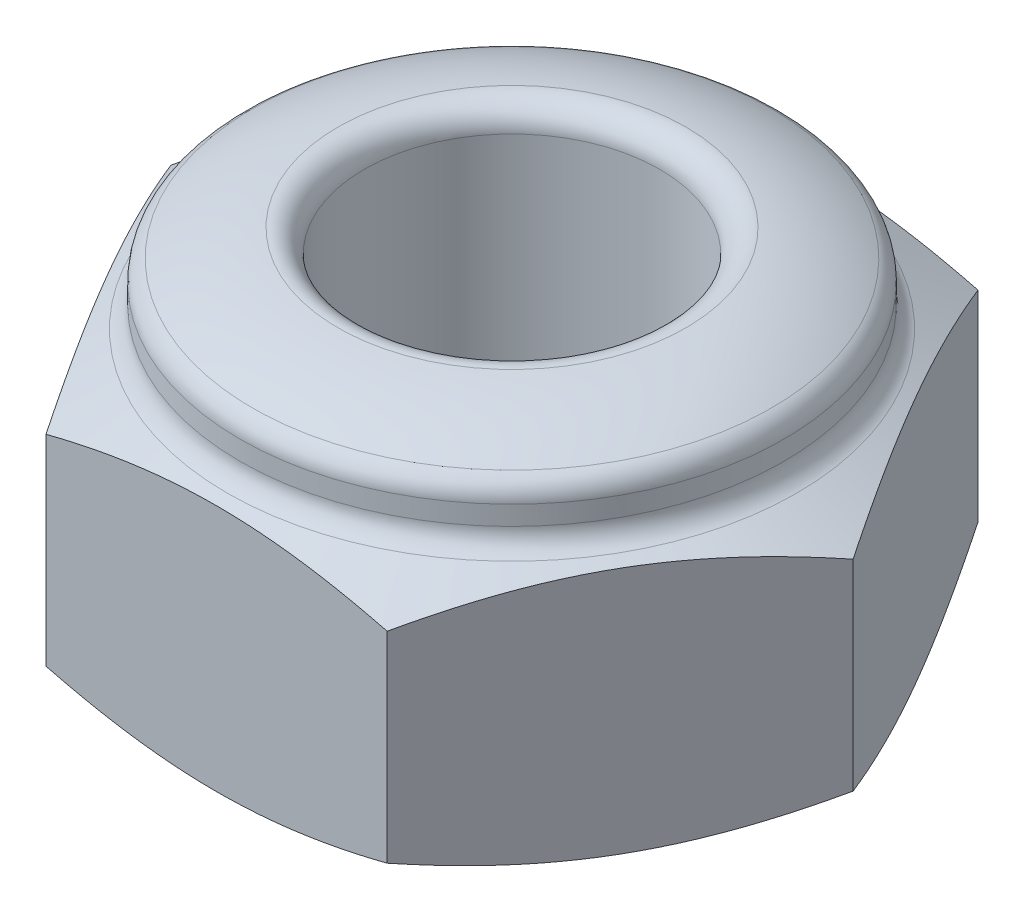
SolidWorks part; units mm, degrees
ref_plane "前视基准面" through (0, 0, 0) normal (0, 0, 1) x (1, 0, 0)
ref_plane "上视基准面" through (0, 0, 0) normal (0, 1, 0) x (1, 0, 0)
ref_plane "右视基准面" through (0, 0, 0) normal (1, 0, 0) x (0, 0, -1)
sketch "草图1" plane through (0, 0, 0) normal (0, 1, 0) x (1, 0, 0)
  line L1 (2.8868, 0) -> (1.4434, 2.5)
  line L2 (1.4434, 2.5) -> (-1.4434, 2.5)
  line L3 (-1.4434, 2.5) -> (-2.8868, 0)
  line L4 (-2.8868, 0) -> (-1.4434, -2.5)
  line L5 (-1.4434, -2.5) -> (1.4434, -2.5)
  line L6 (1.4434, -2.5) -> (2.8868, 0)
  circle A0 centre (0, 0) radius 2.5 construction
  circle A1 centre (0, 0) radius 1.25
  dimension "D2" = 2.5
  dimension "D1" = 5
extrude "凸台-拉伸1" add sketch "草图1" along normal mid plane 2.3
sketch "草图2" plane through (0, 0, 0) normal (0, 0, 1) x (1, 0, 0)
  line L0 (-2.8868, 0.85) -> (-2.3, 1.15)
  line L1 (-2.8868, 1.15) -> (-2.8868, -1.15) construction
  line L2 (-2.8868, 1.15) -> (-1.4434, 1.15) construction
  line L3 (-2.3, 1.15) -> (-2.8868, 1.15)
  line L4 (-2.8868, 1.15) -> (-2.8868, 0.85)
  line L5 (0, 1.15) -> (0, -1.15) construction
  line L6 (-1.4434, 1.15) -> (1.4434, 1.15) construction
  line L7 (-1.4434, -1.15) -> (1.4434, -1.15) construction
  dimension "D1" = 4.6
  dimension "D2" = 0.3
revolve "切除-旋转1" cut sketch "草图2" angle 360 about L5
mirror "镜向1" about plane through (0, 0, 0) normal (0, 1, 0) of "切除-旋转1"
sketch "草图3" plane through (0, 0, 0) normal (1, 0, 0) x (0, 0, -1)
  line L0 (-2.3, 1.15) -> (-2.3, 1.55)
  line L1 (-1.25, 1.15) -> (-1.25, 1.85)
  line L2 (2.3, 1.15) -> (-2.3, 1.15) construction
  line L3 (-1.25, 1.85) -> (-2.3, 1.85) construction
  line L4 (0, 1.15) -> (0, -1.15) construction
  line L5 (1.25, 1.15) -> (-1.25, 1.15) construction
  line L6 (-2.3, -1.15) -> (2.3, -1.15) construction
  line L7 (-2.3, 1.15) -> (-1.25, 1.15)
  arc A0 (-2.3, 1.55) -> (-1.25, 1.85) centre (-1.25, -0.1375) cw
  dimension "D1" = 2.5
  dimension "D2" = 3
  dimension "D3" = 0.4
revolve "旋转1" add sketch "草图3" angle 360 about L4
fillet "圆角1" radius 0.2 3 edges at (0, 1.15, 2.3) (0, 1.55, 2.3) (0, 1.85, 1.25)
